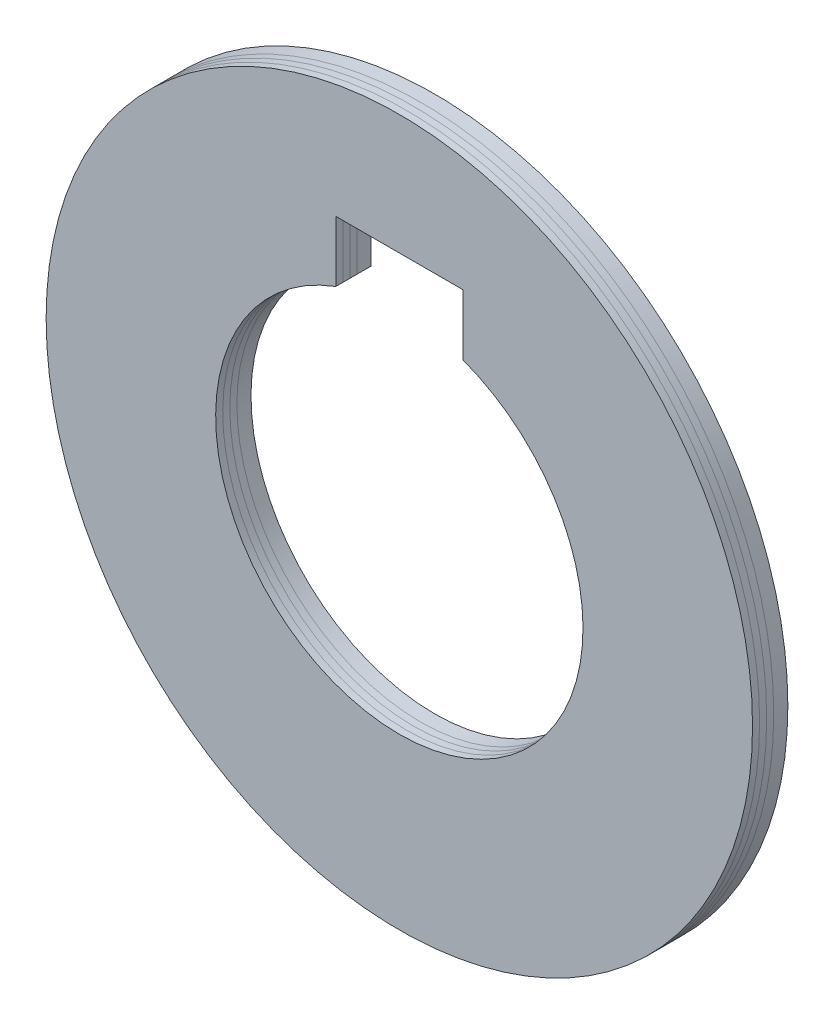
SolidWorks part; units mm, degrees
material "Ст 3 ГОСТ 380-2005"
ref_plane "Спереди" through (0, 0, 0) normal (0, 0, 1) x (1, 0, 0)
ref_plane "Сверху" through (0, 0, 0) normal (0, 1, 0) x (1, 0, 0)
ref_plane "Слева" through (0, 0, 0) normal (1, 0, 0) x (0, 0, -1)
sketch "Эскиз1" plane through (0, 0, 0) normal (0, 0, 1) x (1, 0, 0)
  line L0 (0, 16.5) -> (0, 0) construction
  line L1 (-4.5, 16.5) -> (4.5, 16.5)
  line L2 (-4.5, 16.5) -> (-4.5, 12.1963)
  line L4 (4.5, 16.5) -> (4.5, 12.1963)
  arc A0 (-4.5, 12.1963) -> (4.5, 12.1963) centre (0, 0) ccw
  circle A1 centre (0, 0) radius 25
  dimension "D1" = 26
  dimension "D4" = 50
  dimension "D5" = 7.8974
  dimension "D2" = 9
  dimension "D3" = 16.5
extrude "Вытянуть1" add sketch "Эскиз1" along normal blind 2.5
sketch "Эскиз2" plane through (0, 0, 0) normal (0, 1, 0) x (1, 0, 0)
  line L0 (-25, 0) -> (-25, -2.5) construction
  line L1 (-25, 0) -> (-25, -2.5)
  line L2 (25, -2.5) -> (25, 0) construction
  line L3 (25, -2.5) -> (25, 0)
  line L4 (-25, -1) -> (25, -1)
  line L5 (-25, -1.5) -> (25, -1.5)
  line L6 (-25, -2) -> (25, -2)
  line L7 (25, 0) -> (-25, 0) construction
  dimension "D1" = 1
  dimension "D2" = 0.5
  dimension "D3" = 0.5
split "Разделить1" trim tools "Эскиз2" resulting bodies 102 103 104 105
